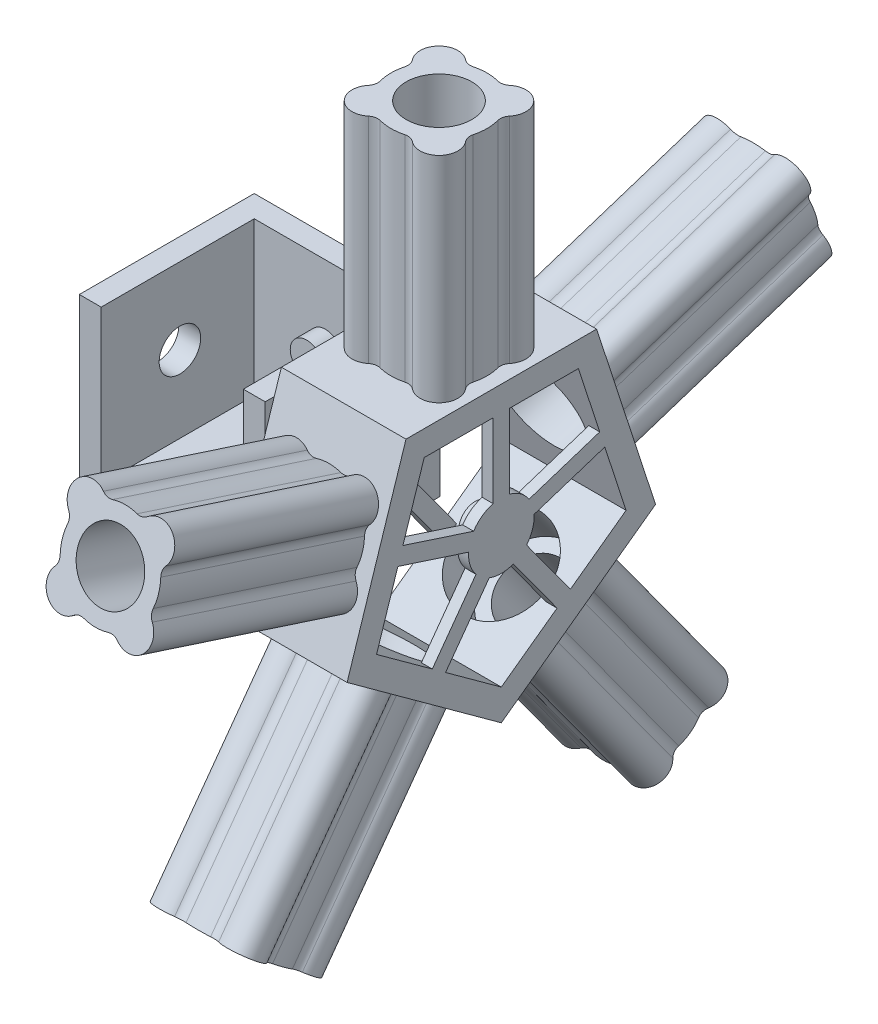
SolidWorks part; units mm, degrees
material "AISI 1020"
ref_plane "Front Plane" through (0, 0, 0) normal (0, 0, 1) x (1, 0, 0)
ref_plane "Top Plane" through (0, 0, 0) normal (0, 1, 0) x (1, 0, 0)
ref_plane "Right Plane" through (0, 0, 0) normal (1, 0, 0) x (0, 0, -1)
sketch "Sketch1" plane through (0, 0, 0) normal (0, 1, 0) x (1, 0, 0)
  line L1 (0, 0) -> (85, 0)
  line L2 (0, 0) -> (0, 80)
  line L3 (0, 80) -> (85, 80)
  line L4 (85, 0) -> (85, 80)
  dimension "D1" = 85
  dimension "D2" = 80
extrude "Boss-Extrude1" add sketch "Sketch1" along normal blind 7.5 contours L2 L1 L4 L3
sketch "Sketch2" plane through (0, 7.5, 0) normal (0, 1, 0) x (1, 0, 0)
  line L0 (0, 0) -> (0, 80)
  line L1 (0, 80) -> (85, 80)
  line L2 (85, 80) -> (85, 0)
  line L3 (85, 0) -> (75, 0)
  line L4 (0, 0) -> (85, 0) construction
  line L5 (0, 0) -> (10, 0)
  line L6 (10, 0) -> (10, 70)
  line L7 (75, 0) -> (75, 69.9981)
  line L8 (10, 70) -> (75, 69.9981)
  dimension "D1" = 70
  dimension "D2" = 10
  dimension "D3" = 10
  dimension "D4" = 69.9981
  dimension "D5" = 65
extrude "Boss-Extrude2" add sketch "Sketch2" along normal blind 70
sketch "Sketch3" plane through (0.0021, 0, -70.0003) normal (0, 0, 1) x (1, 0, 0)
  line L0 (9.9979, 77.5) -> (9.9979, 7.5) construction
  line L1 (9.9979, 77.5) -> (74.9979, 77.5) construction
  circle A0 centre (42.4979, 42.5) radius 7.5
  dimension "D1" = 32.5
  dimension "D2" = 35
extrude "Boss-Extrude3" add sketch "Sketch3" along normal blind 8.54 contours A0
sketch "Sketch4" plane through (10, 0, 0) normal (1, 0, 0) x (0, 0, -1)
  line L0 (80, 77.5) -> (80, 0) construction
  line L1 (0, 0) -> (80, 0) construction
  circle A0 centre (36, 42.5) radius 9.5
  dimension "D1" = 44
  dimension "D3" = 19
  dimension "D2" = 42.5
extrude "Cut-Extrude1" cut sketch "Sketch4" against normal blind 15
sketch "Sketch5" plane through (75, 0, 0) normal (-1, 0, 0) x (0, 0, 1)
  line L0 (0, 77.5) -> (0, 0) construction
  line L1 (0, 0) -> (-80, 0) construction
  circle A0 centre (-36, 42.5) radius 7.5
  dimension "D1" = 36
  dimension "D2" = 42.5
extrude "Cut-Extrude2" cut sketch "Sketch5" against normal blind 15 contours A0
sketch "Sketch6" plane through (85, 0, 0) normal (1, 0, 0) x (0, 0, -1)
  circle A0 centre (36, 42.5) radius 10
  circle A1 centre (36, 42.5) radius 7.5
extrude "Boss-Extrude4" add sketch "Sketch6" along normal blind 15 contours A0 | A1
sketch "Sketch7" plane through (100, 0, 0) normal (1, 0, 0) x (0, 0, -1)
  line L0 (81.0064, 61.0665) -> (48.654, 50.5545)
  line L1 (-7.5926, 102.5) -> (-34.5342, 19.582)
  line L2 (-34.5342, 19.582) -> (36, -31.6641)
  line L3 (36, -31.6641) -> (106.5342, 19.582)
  line L4 (106.5342, 19.582) -> (79.5926, 102.5)
  line L5 (79.5926, 102.5) -> (-7.5926, 102.5)
  line L6 (0.7329, 91.041) -> (-9.0064, 61.0665)
  line L7 (-21.0634, 23.959) -> (4.4345, 5.4337)
  line L8 (36, -17.5) -> (61.4979, 1.0253)
  line L9 (93.0634, 23.959) -> (83.3241, 53.9335)
  line L10 (71.2671, 91.041) -> (39.75, 91.041)
  line L12 (39.75, 91.041) -> (39.75, 57.0237)
  line L13 (32.25, 91.041) -> (32.25, 57.0237)
  line L14 (83.3241, 53.9335) -> (50.9717, 43.4216)
  line L15 (67.5655, 5.4337) -> (47.5706, 32.9543)
  line L16 (61.4979, 1.0253) -> (41.503, 28.5459)
  line L17 (10.5021, 1.0253) -> (30.497, 28.5459)
  line L18 (4.4345, 5.4337) -> (24.4294, 32.9543)
  line L19 (-11.3241, 53.9335) -> (21.0283, 43.4216)
  line L20 (-9.0064, 61.0665) -> (23.346, 50.5545)
  line L21 (-11.3241, 53.9335) -> (-21.0634, 23.959)
  line L22 (10.5021, 1.0253) -> (36, -17.5)
  line L23 (67.5655, 5.4337) -> (93.0634, 23.959)
  line L24 (81.0064, 61.0665) -> (71.2671, 91.041)
  line L25 (32.25, 91.041) -> (0.7329, 91.041)
  circle A0 centre (36, 42.5) radius 40 construction
  circle A1 centre (36, 42.5) radius 7.5
  arc A2 (4.5426, 50.0925) -> (15.0132, 17.8674) centre (36, 42.5) ccw construction
  arc A3 (21.0283, 43.4216) -> (24.4294, 32.9543) centre (36, 42.5) ccw
  arc A4 (19.0583, 14.9284) -> (52.9417, 14.9284) centre (36, 42.5) ccw construction
  arc A5 (56.9868, 17.8674) -> (67.4574, 50.0925) centre (36, 42.5) ccw construction
  arc A6 (65.9123, 54.8478) -> (38.5, 74.764) centre (36, 42.5) ccw construction
  arc A7 (33.5, 74.764) -> (6.0877, 54.8478) centre (36, 42.5) ccw construction
  arc A8 (32.25, 57.0237) -> (23.346, 50.5545) centre (36, 42.5) ccw
  arc A9 (48.654, 50.5545) -> (39.75, 57.0237) centre (36, 42.5) ccw
  arc A10 (47.5706, 32.9543) -> (50.9717, 43.4216) centre (36, 42.5) ccw
  arc A11 (30.497, 28.5459) -> (41.503, 28.5459) centre (36, 42.5) ccw
  point P40 (36, 42.5)
  dimension "D1" = 5
extrude "Boss-Extrude7" add sketch "Sketch7" along normal blind 5
sketch "Sketch11" plane through (105, 0, 0) normal (1, 0, 0) x (0, 0, -1)
  line L1 (79.5926, 102.5) -> (-7.5926, 102.5)
  line L2 (-7.5926, 102.5) -> (-34.5342, 19.582)
  line L3 (-34.5342, 19.582) -> (36, -31.6641)
  line L4 (36, -31.6641) -> (106.5342, 19.582)
  line L5 (106.5342, 19.582) -> (79.5926, 102.5)
  line L6 (71.2671, 91.041) -> (0.7329, 91.041)
  line L7 (0.7329, 91.041) -> (-21.0634, 23.959)
  line L8 (-21.0634, 23.959) -> (36, -17.5)
  line L9 (36, -17.5) -> (93.0634, 23.959)
  line L10 (93.0634, 23.959) -> (71.2671, 91.041)
  circle A0 centre (36, 42.5) radius 60 construction
  circle A1 centre (36, 42.5) radius 48.541 construction
extrude "Boss-Extrude14" add sketch "Sketch11" along normal blind 47
sketch "Sketch12" plane through (152, 0, 0) normal (1, 0, 0) x (0, 0, -1)
  line L0 (0.7329, 91.041) -> (32.25, 91.041)
  line L1 (79.5926, 102.5) -> (-7.5926, 102.5)
  line L2 (-7.5926, 102.5) -> (-34.5342, 19.582)
  line L3 (-34.5342, 19.582) -> (36, -31.6641)
  line L4 (36, -31.6641) -> (106.5342, 19.582)
  line L5 (106.5342, 19.582) -> (79.5926, 102.5)
  line L6 (32.25, 91.041) -> (32.25, 57.0237)
  line L7 (39.75, 57.0237) -> (39.75, 91.041)
  line L8 (39.75, 91.041) -> (71.2671, 91.041)
  line L9 (71.2671, 91.041) -> (81.0064, 61.0665)
  line L10 (81.0064, 61.0665) -> (48.654, 50.5545)
  line L11 (50.9717, 43.4216) -> (83.3241, 53.9335)
  line L12 (83.3241, 53.9335) -> (93.0634, 23.959)
  line L13 (93.0634, 23.959) -> (67.5655, 5.4337)
  line L14 (67.5655, 5.4337) -> (47.5706, 32.9543)
  line L15 (41.503, 28.5459) -> (61.4979, 1.0253)
  line L16 (61.4979, 1.0253) -> (36, -17.5)
  line L17 (36, -17.5) -> (10.5021, 1.0253)
  line L18 (10.5021, 1.0253) -> (30.497, 28.5459)
  line L19 (21.0283, 43.4216) -> (-11.3241, 53.9335)
  line L20 (-11.3241, 53.9335) -> (-21.0634, 23.959)
  line L21 (-21.0634, 23.959) -> (4.4345, 5.4337)
  line L22 (4.4345, 5.4337) -> (24.4294, 32.9543)
  line L23 (23.346, 50.5545) -> (-9.0064, 61.0665)
  line L24 (-9.0064, 61.0665) -> (0.7329, 91.041)
  circle A0 centre (36, 42.5) radius 60 construction
  arc A6 (21.0283, 43.4216) -> (24.4294, 32.9543) centre (36, 42.5) ccw
  arc A7 (30.497, 28.5459) -> (41.503, 28.5459) centre (36, 42.5) ccw
  arc A8 (47.5706, 32.9543) -> (50.9717, 43.4216) centre (36, 42.5) ccw
  arc A9 (48.654, 50.5545) -> (39.75, 57.0237) centre (36, 42.5) ccw
  arc A10 (32.25, 57.0237) -> (23.346, 50.5545) centre (36, 42.5) ccw
extrude "Boss-Extrude15" add sketch "Sketch12" along normal blind 5
sketch "Sketch13" plane through (152, 0, 0) normal (-1, 0, 0) x (0, 0, 1)
  circle A0 centre (-36, 42.5) radius 7.5
extrude "Boss-Extrude16" add sketch "Sketch13" along normal blind 7
sketch "Sketch14" plane through (0, 102.5, 0) normal (0, 1, 0) x (1, 0, 0)
  circle A0 centre (128.5, 36) radius 15
  arc A1 (122.8839, 14.7289) -> (134.1161, 14.7289) centre (128.5, 36) ccw
  arc A2 (106.2585, 25.9341) -> (118.4341, 13.7585) centre (112.9437, 20.4437) ccw
  arc A3 (118.4341, 58.2415) -> (106.2585, 46.0659) centre (112.9437, 51.5563) ccw
  arc A4 (150.7415, 46.0659) -> (138.5659, 58.2415) centre (144.0563, 51.5563) ccw
  arc A5 (138.5659, 13.7585) -> (150.7415, 25.9341) centre (144.0563, 20.4437) ccw
  arc A6 (107.2289, 41.6161) -> (107.2289, 30.3839) centre (128.5, 36) ccw
  arc A7 (134.1161, 57.2711) -> (122.8839, 57.2711) centre (128.5, 36) ccw
  arc A8 (149.7711, 30.3839) -> (149.7711, 41.6161) centre (128.5, 36) ccw
  arc A9 (106.2585, 25.9341) -> (107.2289, 30.3839) centre (102.3946, 29.1075) ccw
  arc A10 (118.4341, 13.7585) -> (122.8839, 14.7289) centre (121.6075, 9.8946) cw
  arc A11 (138.5659, 13.7585) -> (134.1161, 14.7289) centre (135.3925, 9.8946) ccw
  arc A12 (150.7415, 25.9341) -> (149.7711, 30.3839) centre (154.6054, 29.1075) cw
  arc A13 (150.7415, 46.0659) -> (149.7711, 41.6161) centre (154.6054, 42.8925) ccw
  arc A14 (138.5659, 58.2415) -> (134.1161, 57.2711) centre (135.3925, 62.1054) cw
  arc A15 (118.4341, 58.2415) -> (122.8839, 57.2711) centre (121.6075, 62.1054) ccw
  arc A16 (106.2585, 46.0659) -> (107.2289, 41.6161) centre (102.3946, 42.8925) cw
  point P17 (128.5, 36)
  dimension "D1" = 4
  dimension "D2" = 5
extrude "Boss-Extrude17" add sketch "Sketch14" along normal blind 98
sketch "Sketch15" plane through (0, 102.5, 0) normal (0, 1, 0) x (1, 0, 0)
  circle A0 centre (128.5, 36) radius 15
extrude "Cut-Extrude3" cut sketch "Sketch15" against normal blind 12
pattern_circular "CirPattern1" count 5 over 360 about axis through (0, 42.5, -36) along (1, 0, 0) of "Cut-Extrude3", "Boss-Extrude17"
sketch "Sketch16" plane through (0, 91.041, 0) normal (0, -1, 0) x (-1, 0, 0)
  line L0 (-157, 36) -> (-100, 36) construction
  circle A0 centre (-128.5, 36) radius 21
extrude "Cut-Extrude4" cut sketch "Sketch16" against normal blind 25
pattern_circular "CirPattern2" count 5 over 360 about axis through (0, 42.5, -36) along (1, 0, 0) of "Cut-Extrude4"
